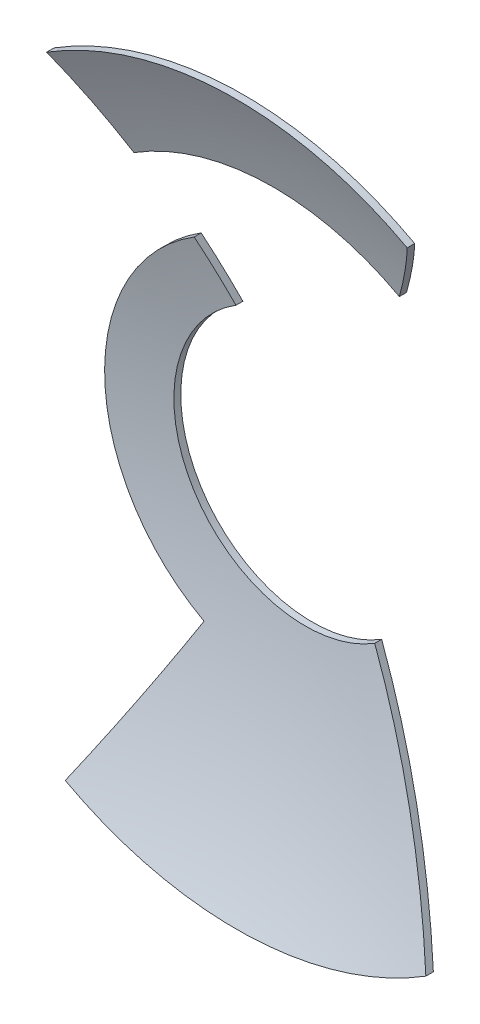
SolidWorks part; units mm, degrees
ref_plane "前视基准面" through (0, 0, 0) normal (0, 0, 1) x (1, 0, 0)
ref_plane "上视基准面" through (0, 0, 0) normal (0, 1, 0) x (1, 0, 0)
ref_plane "右视基准面" through (0, 0, 0) normal (1, 0, 0) x (0, 0, -1)
sketch "草图1" plane through (0, 0, 0) normal (0, 0, 1) x (1, 0, 0)
  line L0 (106.6667, -113.1573) -> (533.3333, -113.1573) construction
sketch "草图2" plane through (0, 0, 0) normal (0, 0, 1) x (1, 0, 0)
  line L0 (-27.7974, 44.7579) -> (-20.4626, 32.9477)
  line L1 (25.0649, 46.3434) -> (18.4511, 34.1149)
  line L2 (-14.6657, 23.6139) -> (-10.17, 16.3752)
  line L4 (10.17, -16.3752) -> (27.7974, -44.7579)
  line L5 (-13.2241, -24.4504) -> (-25.0649, -46.3434)
  arc A0 (-25.0649, -46.3434) -> (27.7974, -44.7579) centre (0, 0) ccw
  arc A1 (-10.17, 16.3752) -> (10.17, -16.3752) centre (0, 0) ccw
  arc A2 (-14.6657, 23.6139) -> (-13.2241, -24.4504) centre (0, 0) ccw
  arc A3 (18.4511, 34.1149) -> (-20.4626, 32.9477) centre (0, 0) ccw
  arc A5 (25.0649, 46.3434) -> (-27.7974, 44.7579) centre (0, 0) ccw
sketch "草图3" plane through (0, 0, 0) normal (0, 0, 1) x (1, 0, 0)
  line L0 (0, 183.5567) -> (0, -201.9307) construction
  line L1 (0, -125.2) -> (0, 125.2)
  arc A0 (0, 125.2) -> (0, -125.2) centre (0, 0) ccw
revolve "旋转1" add sketch "草图3" angle 180 about L0
shell "抽壳1" thickness 1
extrude "切除-拉伸1" cut sketch "草图2" against normal blind 181 flip side to cut
